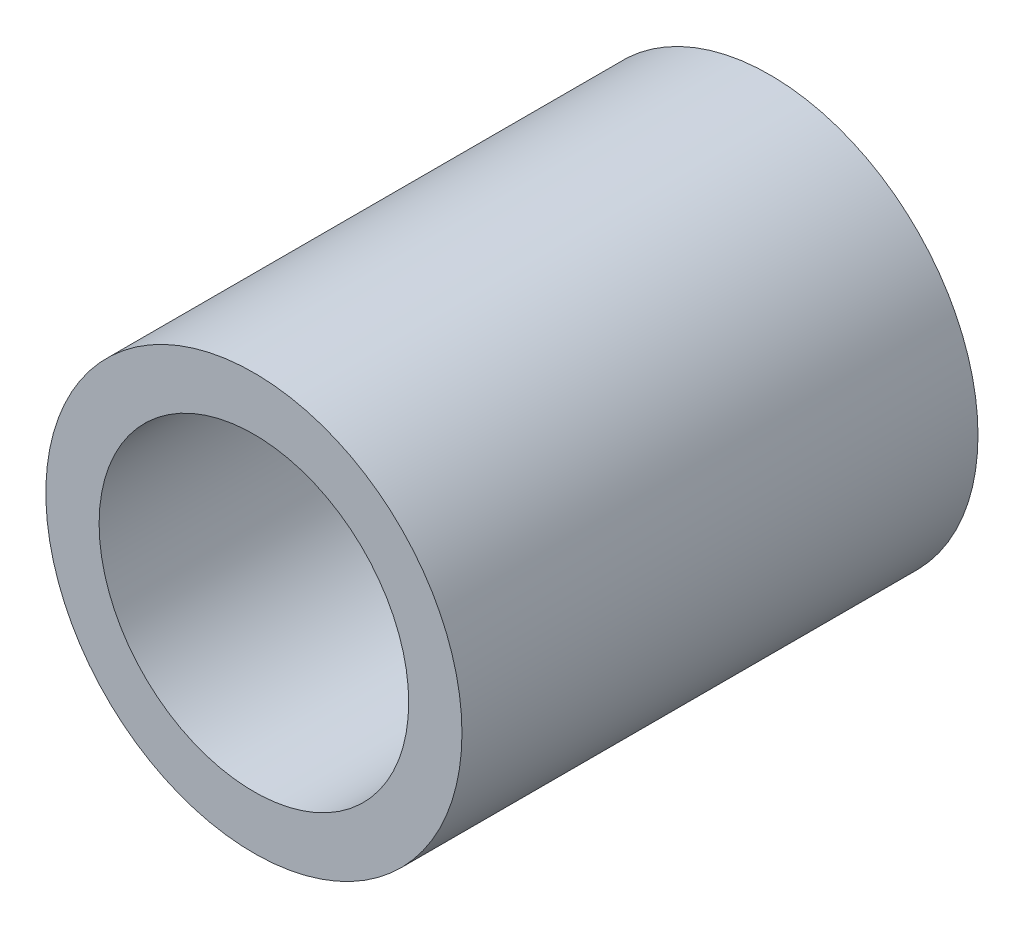
SolidWorks part; units mm, degrees
material "841 Oilite Bronze"
ref_plane "Front Plane" through (0, 0, 0) normal (0, 0, 1) x (1, 0, 0)
ref_plane "Top Plane" through (0, 0, 0) normal (0, 1, 0) x (1, 0, 0)
ref_plane "Right Plane" through (0, 0, 0) normal (1, 0, 0) x (0, 0, -1)
sketch "Sketch1" plane through (0, 0, 0) normal (0, 0, 1) x (1, 0, 0)
  circle A0 centre (0, 0) radius 3.2004
  circle A1 centre (0, 0) radius 2.3812
  dimension "OD" = 6.4008
  dimension "ID" = 4.7625
sketch "Sketch2" plane through (0, 0, 0) normal (1, 0, 0) x (0, 0, -1)
  line L2 (3.9688, 0) -> (-3.9688, 0) construction
  line L4 (-3.9688, -3.2004) -> (-3.9688, 3.2004) construction
  line L5 (-3.9688, -2.3812) -> (3.9687, -2.3812)
  line L6 (3.9688, 2.3812) -> (-3.9688, 2.3812)
  line L7 (3.9688, -3.2004) -> (3.9688, 3.2004) construction
  line L8 (-3.9688, 3.2004) -> (3.9688, 3.2004) construction
  line L9 (-3.9688, -3.2004) -> (3.9688, -3.2004) construction
  line L10 (0, 3.2004) -> (0, -3.2004) construction
  line L11 (0, 2.3812) -> (0, -2.3812) construction
  point P4 (0, -2.3812)
  point P7 (0, 2.3812)
  point P8 (0, 0)
  point P12 (-3.9688, 0)
  point P15 (3.9688, 0)
  point P16 (0, -3.2004)
  point P17 (0, 3.2004)
  dimension "Length" = 7.9375
sketch "Sketch5" plane through (0, 0, 0) normal (0, 0, 1) x (1, 0, 0)
  circle A1 centre (0, 0) radius 2.3812
  circle A2 centre (0, 0) radius 2.3812
  circle A3 centre (0, 0) radius 3.2004
  circle A4 centre (0, 0) radius 3.2004
  dimension "D1" = 0
  dimension "D2" = 0
extrude "Boss-Extrude1" add sketch "Sketch5" along normal mid plane 7.9375
equation "\"D1@Boss-Extrude1\" = \"Length@Sketch2\""
